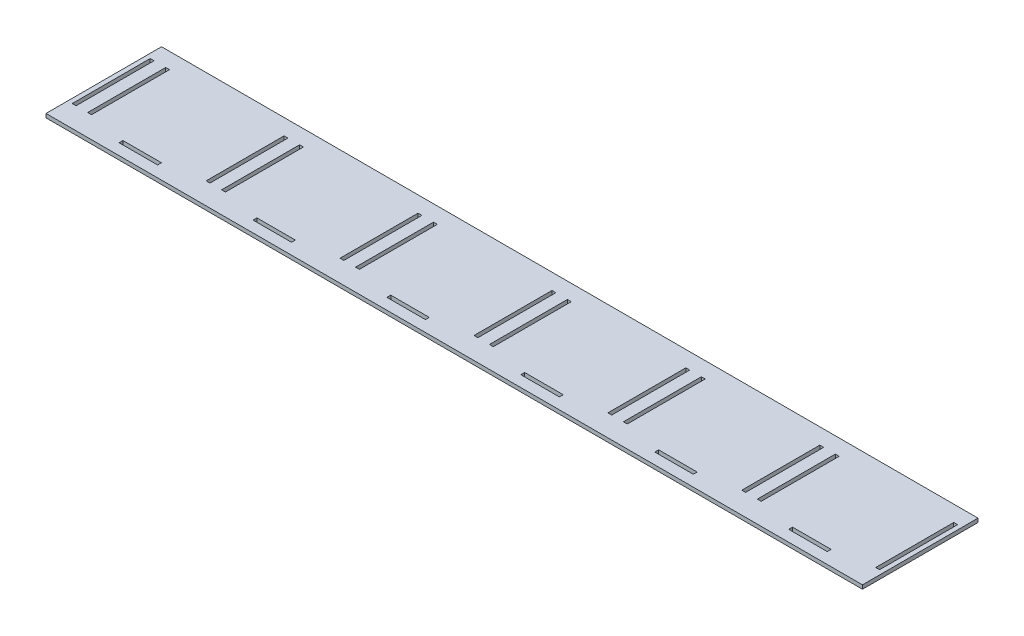
SolidWorks part; units mm, degrees
ref_plane "Front Plane" through (0, 0, 0) normal (0, 0, 1) x (1, 0, 0)
ref_plane "Top Plane" through (0, 0, 0) normal (0, 1, 0) x (1, 0, 0)
ref_plane "Right Plane" through (0, 0, 0) normal (1, 0, 0) x (0, 0, -1)
sketch "Sketch1" plane through (0, 0, 0) normal (0, 1, 0) x (1, 0, 0)
  line L0 (79.95, -48.75) -> (81.95, -48.75)
  line L1 (0, 0) -> (424, 0)
  line L2 (0, 0) -> (0, -60)
  line L3 (0, -60) -> (424, -60)
  line L4 (424, 0) -> (424, -60)
  line L5 (149.5, -48.75) -> (151.5, -48.75)
  line L6 (4.35, -8.25) -> (4.35, -48.75)
  line L7 (71.9, -8.25) -> (71.9, -48.75)
  line L8 (12.4, -8.25) -> (12.4, -48.75)
  line L9 (10.4, -8.25) -> (12.4, -8.25)
  line L10 (358.15, -8.25) -> (360.15, -8.25)
  line L11 (79.95, -8.25) -> (81.95, -8.25)
  line L12 (73.9, -8.25) -> (73.9, -48.75)
  line L13 (10.4, -8.25) -> (10.4, -48.75)
  line L14 (350.1, -8.25) -> (352.1, -8.25)
  line L15 (288.6, -8.25) -> (290.6, -8.25)
  line L16 (79.95, -8.25) -> (79.95, -48.75)
  line L17 (81.95, -8.25) -> (81.95, -48.75)
  line L18 (219.05, -48.75) -> (221.05, -48.75)
  line L19 (288.6, -48.75) -> (290.6, -48.75)
  line L20 (141.45, -8.25) -> (141.45, -48.75)
  line L21 (143.45, -8.25) -> (143.45, -48.75)
  line L22 (71.9, -48.75) -> (73.9, -48.75)
  line L23 (101.7, -54.2) -> (101.7, -52.2)
  line L24 (149.5, -8.25) -> (149.5, -48.75)
  line L25 (151.5, -8.25) -> (151.5, -48.75)
  line L26 (101.7, -52.2) -> (121.7, -52.2)
  line L27 (32.15, -54.2) -> (52.15, -54.2)
  line L28 (211, -8.25) -> (211, -48.75)
  line L29 (213, -8.25) -> (213, -48.75)
  line L30 (101.7, -54.2) -> (121.7, -54.2)
  line L31 (52.15, -52.2) -> (52.15, -54.2)
  line L32 (219.05, -8.25) -> (219.05, -48.75)
  line L33 (221.05, -8.25) -> (221.05, -48.75)
  line L34 (32.15, -52.2) -> (52.15, -52.2)
  line L35 (32.15, -54.2) -> (32.15, -52.2)
  line L36 (280.55, -8.25) -> (280.55, -48.75)
  line L37 (282.55, -8.25) -> (282.55, -48.75)
  line L40 (288.6, -8.25) -> (288.6, -48.75)
  line L41 (290.6, -8.25) -> (290.6, -48.75)
  line L42 (121.7, -52.2) -> (121.7, -54.2)
  line L43 (171.25, -54.2) -> (171.25, -52.2)
  line L44 (350.1, -8.25) -> (350.1, -48.75)
  line L45 (352.1, -8.25) -> (352.1, -48.75)
  line L46 (171.25, -52.2) -> (191.25, -52.2)
  line L47 (171.25, -54.2) -> (191.25, -54.2)
  line L48 (358.15, -8.25) -> (358.15, -48.75)
  line L49 (360.15, -8.25) -> (360.15, -48.75)
  line L50 (191.25, -52.2) -> (191.25, -54.2)
  line L51 (240.8, -54.2) -> (240.8, -52.2)
  line L52 (419.65, -8.25) -> (419.65, -48.75)
  line L53 (421.65, -8.25) -> (421.65, -48.75)
  line L54 (240.8, -52.2) -> (260.8, -52.2)
  line L55 (2.35, -8.25) -> (2.35, -48.75)
  line L56 (240.8, -54.2) -> (260.8, -54.2)
  line L57 (10.4, -48.75) -> (12.4, -48.75)
  line L58 (2.35, -48.75) -> (4.35, -48.75)
  line L59 (2.35, -8.25) -> (4.35, -8.25)
  line L60 (71.9, -8.25) -> (73.9, -8.25)
  line L61 (280.55, -8.25) -> (282.55, -8.25)
  line L62 (219.05, -8.25) -> (221.05, -8.25)
  line L63 (211, -8.25) -> (213, -8.25)
  line L64 (149.5, -8.25) -> (151.5, -8.25)
  line L65 (141.45, -8.25) -> (143.45, -8.25)
  line L66 (141.45, -48.75) -> (143.45, -48.75)
  line L67 (211, -48.75) -> (213, -48.75)
  line L68 (280.55, -48.75) -> (282.55, -48.75)
  line L69 (350.1, -48.75) -> (352.1, -48.75)
  line L70 (419.65, -8.25) -> (421.65, -8.25)
  line L71 (358.15, -48.75) -> (360.15, -48.75)
  line L72 (419.65, -48.75) -> (421.65, -48.75)
  line L73 (358.15, -48.75) -> (360.15, -48.75)
  line L74 (260.8, -52.2) -> (260.8, -54.2)
  line L75 (310.35, -54.2) -> (310.35, -52.2)
  line L76 (310.35, -52.2) -> (330.35, -52.2)
  line L77 (310.35, -54.2) -> (330.35, -54.2)
  line L78 (330.35, -52.2) -> (330.35, -54.2)
  line L79 (379.9, -54.2) -> (379.9, -52.2)
  line L80 (379.9, -52.2) -> (399.9, -52.2)
  line L81 (379.9, -54.2) -> (399.9, -54.2)
  line L82 (399.9, -52.2) -> (399.9, -54.2)
  point P22 (0, -58)
  point P23 (424, -58)
  point P24 (0, -56)
  point P27 (424, -56)
  point P59 (-144.1331, -129.2938)
  point P60 (247.4863, -129.2938)
  point P63 (2.35, -9.75)
  point P64 (247.4863, -109.0438)
  dimension "D1" = 6
extrude "Boss-Extrude2" add sketch "Sketch1" along normal blind 2 contours L4 L1 L2 L3 L72 L52 L70 L53 L71 L48 L10 L49 L69 L44 L14 L45 L68 L36 L61 L37 L67 L28 L63 L29 L66 L20 L65 L21 L32 L62 L33 L18 L55 L59 L6 L58 L57 L13 L9 L8 L11
